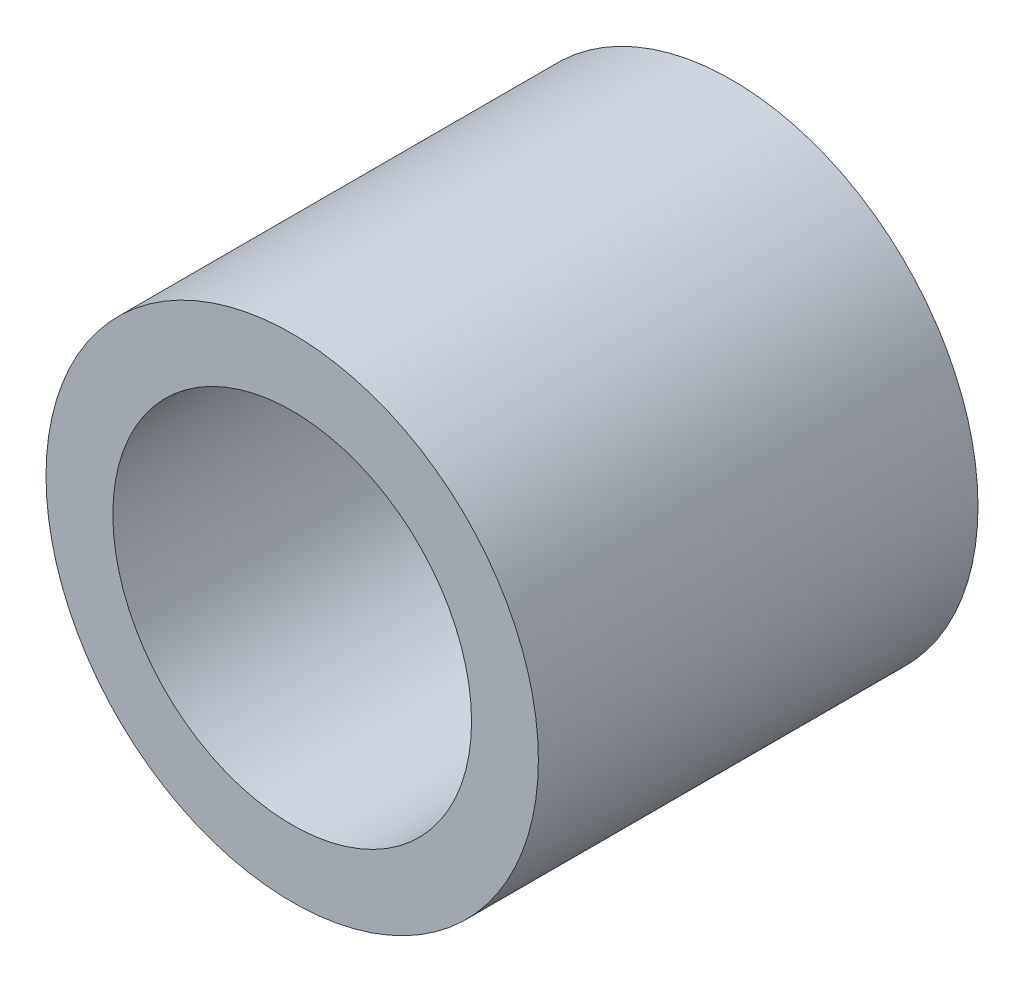
SolidWorks part; units mm, degrees
material "6061 Alloy"
ref_plane "前视基准面" through (0, 0, 0) normal (0, 0, 1) x (1, 0, 0)
ref_plane "上视基准面" through (0, 0, 0) normal (0, 1, 0) x (1, 0, 0)
ref_plane "右视基准面" through (0, 0, 0) normal (1, 0, 0) x (0, 0, -1)
sketch "草图1" plane through (0, 0, 0) normal (0, 0, 1) x (1, 0, 0)
  circle A0 centre (0, 0) radius 14
  circle A1 centre (0, 0) radius 10.2
extrude "凸台-拉伸1" add sketch "草图1" along normal blind 25
